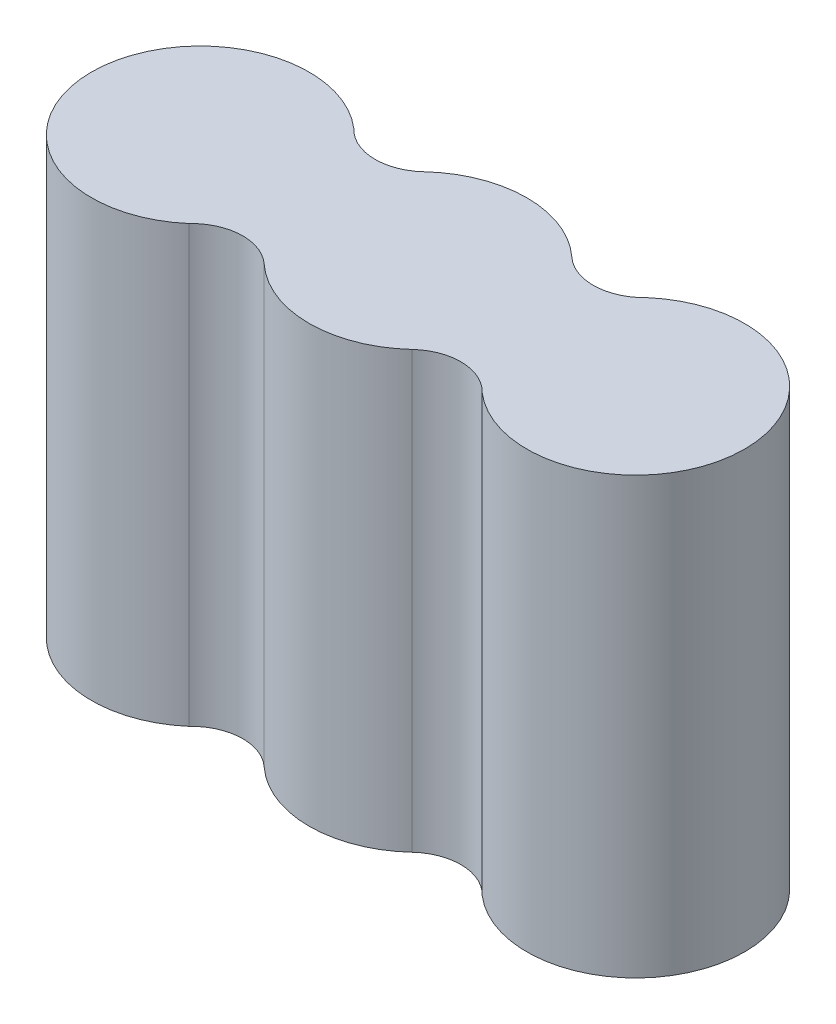
SolidWorks part; units mm, degrees
ref_plane "Alzado" through (0, 0, 0) normal (0, 0, 1) x (1, 0, 0)
ref_plane "Planta" through (0, 0, 0) normal (0, 1, 0) x (1, 0, 0)
ref_plane "Vista lateral" through (0, 0, 0) normal (1, 0, 0) x (0, 0, -1)
sketch "Croquis1" plane through (0, 0, 0) normal (0, 1, 0) x (1, 0, 0)
  line L0 (0, 10.5428) -> (0, 7.5) construction
  line L1 (0, 0) -> (0, 14.2852) construction
  line L3 (0, 0) -> (26.5843, 0) construction
  line L4 (0, -7.5) -> (0, -9.5944) construction
  arc A0 (5.0939, 5.5048) -> (-5.0939, 5.5048) centre (0, 0) ccw
  arc A1 (10.0957, -5.6743) -> (10.0957, 5.6743) centre (15, 0) ccw
  arc A2 (5.0939, 5.5048) -> (10.0957, 5.6743) centre (7.5092, 8.1149) ccw
  arc A3 (5.0939, -5.5048) -> (-5.0939, -5.5048) centre (0, 0) cw
  arc A4 (5.0939, -5.5048) -> (10.0957, -5.6743) centre (7.5092, -8.1149) cw
  arc A5 (-10.0957, -5.6743) -> (-10.0957, 5.6743) centre (-15, 0) cw
  arc A6 (-5.0939, 5.5048) -> (-10.0957, 5.6743) centre (-7.5092, 8.1149) cw
  arc A7 (-5.0939, -5.5048) -> (-10.0957, -5.6743) centre (-7.5092, -8.1149) ccw
  dimension "D1" = 15
  dimension "D3" = 15
  dimension "D2" = 15
extrude "Saliente-Extruir1" add sketch "Croquis1" along normal blind 30
